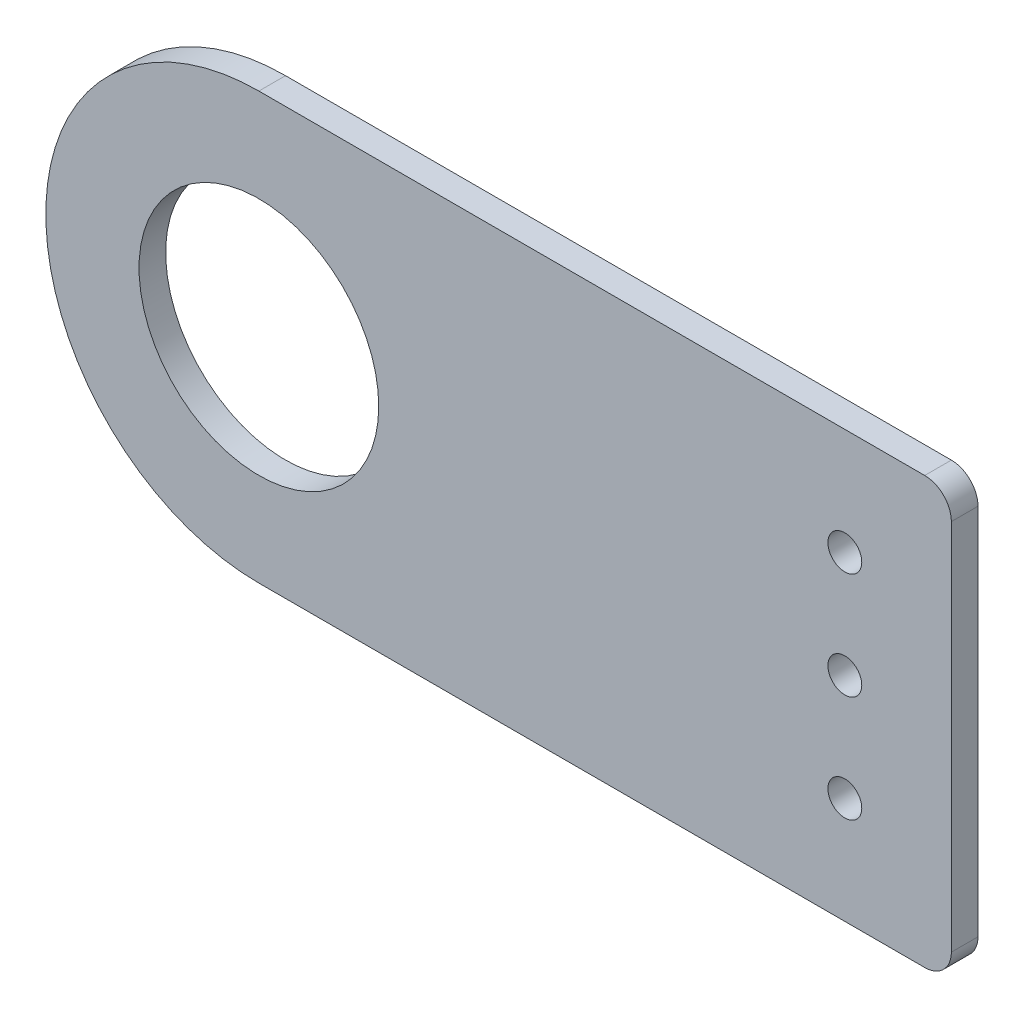
SolidWorks part; units mm, degrees
ref_plane "Front Plane" through (0, 0, 0) normal (0, 0, 1) x (1, 0, 0)
ref_plane "Top Plane" through (0, 0, 0) normal (0, 1, 0) x (1, 0, 0)
ref_plane "Right Plane" through (0, 0, 0) normal (1, 0, 0) x (0, 0, -1)
sketch "Sketch1" plane through (0, 0, 0) normal (0, 0, 1) x (1, 0, 0)
  line L1 (0, 2.0193) -> (0, -2.0193) construction
  line L2 (-69.85, -12.7) -> (-69.85, -58.5975) construction
  line L3 (12.7, -38.1) -> (12.7, 12.7)
  line L4 (-69.85, 12.7) -> (12.7, 12.7)
  line L5 (-69.85, -38.1) -> (12.7, -38.1)
  circle A0 centre (0, 0) radius 2.0193
  circle A1 centre (0, -12.7) radius 2.0193
  circle A2 centre (0, -25.4) radius 2.0193
  circle A3 centre (-69.85, -12.7) radius 14.2875
  arc A4 (-69.85, -38.1) -> (-69.85, 12.7) centre (-69.85, -12.7) cw
  point P17 (12.7, -12.7)
  dimension "D1" = 4.0386
  dimension "D3" = 28.575
  dimension "D5" = 25.4
  dimension "D2" = 3
  dimension "D4" = 69.85
  dimension "D6" = 12.7
extrude "Boss-Extrude1" add sketch "Sketch1" along normal blind 3.175
fillet "Fillet1" radius 3.175 2 edges at (12.7, -38.1, 1.5875) (12.7, 12.7, 1.5875)
